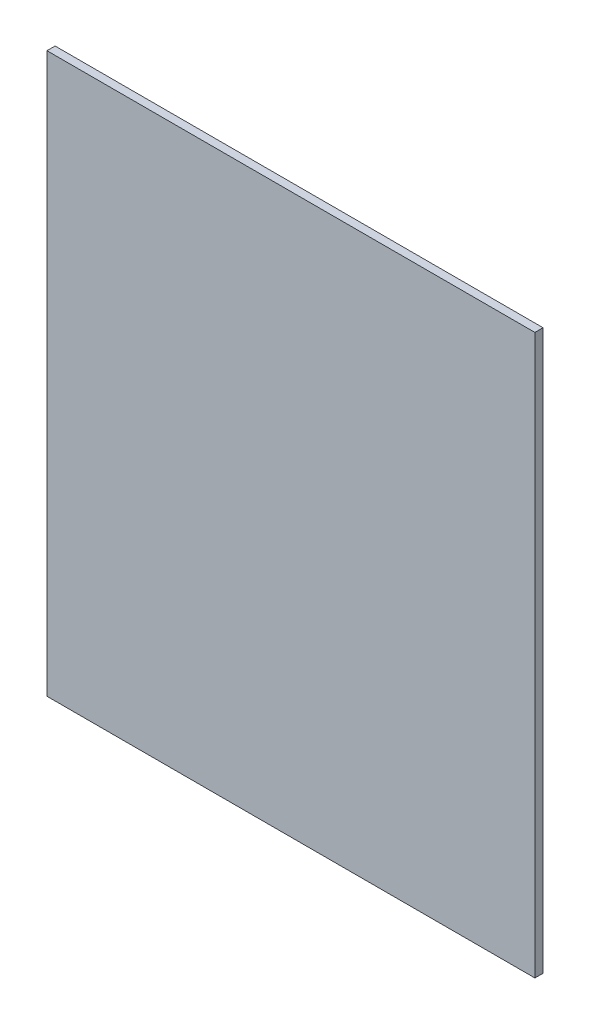
SolidWorks part; units mm, degrees
ref_plane "Front Plane" through (0, 0, 0) normal (0, 0, 1) x (1, 0, 0)
ref_plane "Top Plane" through (0, 0, 0) normal (0, 1, 0) x (1, 0, 0)
ref_plane "Right Plane" through (0, 0, 0) normal (1, 0, 0) x (0, 0, -1)
sketch "Sketch1" plane through (0, 0, 0) normal (0, 0, 1) x (1, 0, 0)
  line L1 (48, -55) -> (-48, -55)
  line L2 (48, -55) -> (48, 55)
  line L3 (48, 55) -> (-48, 55)
  line L4 (-48, -55) -> (-48, 55)
  line L5 (48, -55) -> (-48, 55) construction
  line L6 (48, 55) -> (-48, -55) construction
  point P0 (0, 0)
  dimension "D1" = 110
  dimension "D2" = 96
extrude "Boss-Extrude1" add sketch "Sketch1" along normal blind 1.6
